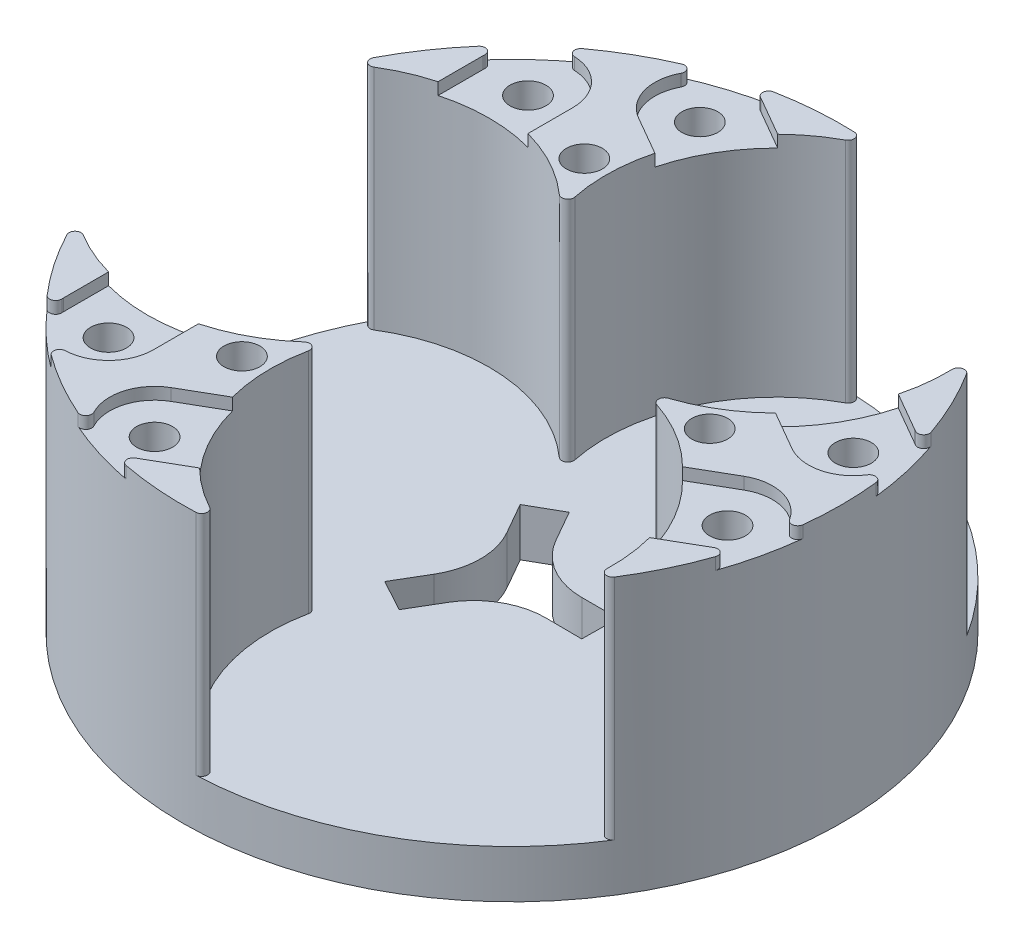
SolidWorks part; units mm, degrees
ref_plane "Front Plane" through (0, 0, 0) normal (0, 0, 1) x (1, 0, 0)
ref_plane "Top Plane" through (0, 0, 0) normal (0, 1, 0) x (1, 0, 0)
ref_plane "Right Plane" through (0, 0, 0) normal (1, 0, 0) x (0, 0, -1)
sketch "Sketch1" plane through (0, 0, 0) normal (0, 1, 0) x (1, 0, 0)
  line L0 (-16.1658, 17.5) -> (-16.1658, -17.5) construction
  line L1 (-3.4432, 3.0103) -> (-4.9292, 5.6165)
  line L2 (-4.9292, 5.6165) -> (-2.3231, 7.1024)
  line L3 (-2.3231, 7.1024) -> (-0.8371, 4.4963)
  line L4 (4.376, 1.4683) -> (7.376, 1.4687)
  line L5 (7.376, 1.4687) -> (7.3529, -1.5312)
  line L6 (7.3529, -1.5312) -> (4.353, -1.5081)
  line L7 (-0.8599, -4.4576) -> (-2.3851, -7.041)
  line L8 (-2.3851, -7.041) -> (-5.0138, -5.5954)
  line L9 (-5.0138, -5.5954) -> (-3.4887, -3.012)
  line L10 (4.3751, 7.4683) -> (0, 0) construction
  line L11 (0, 0) -> (-8.6554, 0.0384) construction
  line L12 (0, 0) -> (4.3068, -7.5079) construction
  circle A0 centre (0, 0) radius 27.5
  circle A1 centre (-16.1658, 17.5) radius 1.5
  circle A2 centre (-16.1658, -17.5) radius 1.5
  circle A3 centre (23.2383, 5.25) radius 1.5
  circle A4 centre (-7.0725, 22.75) radius 1.5
  circle A5 centre (-7.0725, -22.75) radius 1.5
  circle A6 centre (23.2383, -5.25) radius 1.5
  arc A16 (-3.4887, -3.012) -> (-3.4432, 3.0103) centre (-8.6554, 0.0384) ccw
  arc A17 (-0.8371, 4.4963) -> (4.376, 1.4683) centre (4.3751, 7.4683) ccw
  arc A18 (4.353, -1.5081) -> (-0.8599, -4.4576) centre (4.3068, -7.5079) ccw
  circle A19 centre (16.5, 0) radius 1.5
  circle A20 centre (-8.25, -14.2894) radius 1.5
  circle A21 centre (-8.25, 14.2894) radius 1.5
  point P19 (0, 0)
  dimension "D1" = 55
  dimension "D3" = 3
  dimension "D7" = 6
  dimension "D2" = 35
  dimension "D5" = 3
  dimension "D6" = 3
  dimension "D4" = 3
extrude "Boss-Extrude1" add sketch "Sketch1" along normal blind 4
sketch "Sketch2" plane through (0, 4, 0) normal (0, 1, 0) x (1, 0, 0)
  line L0 (-2.2, 0) -> (2.2, 0) construction
  arc A9 (12.569, 0.4746) -> (22.3271, 14.4056) centre (8.0829, 14) ccw
  arc A11 (23.2496, 14.6869) -> (23.2496, -14.6869) centre (0, 0) cw
  arc A22 (22.3271, 14.4056) -> (23.2496, 14.6869) centre (22.8269, 14.4198) cw
  circle A24 centre (23.2383, 5.25) radius 1.5
  circle A25 centre (23.2383, -5.25) radius 1.5
  circle A26 centre (23.2383, 5.25) radius 1.5 construction
  circle A27 centre (-7.0725, -22.75) radius 1.5
  circle A28 centre (-16.1658, -17.5) radius 1.5
  circle A29 centre (-16.1658, 17.5) radius 1.5
  circle A30 centre (-7.0725, 22.75) radius 1.5
  circle A31 centre (16.5, 0) radius 1.5
  circle A32 centre (-8.25, -14.2894) radius 1.5
  circle A33 centre (-8.25, 14.2894) radius 1.5
  arc A35 (12.569, -0.4746) -> (12.569, 0.4746) centre (12.7264, 0) cw
  arc A41 (22.3271, -14.4056) -> (23.2496, -14.6869) centre (22.8269, -14.4198) ccw
  arc A42 (12.569, -0.4746) -> (22.3271, -14.4056) centre (8.0829, -14) cw
  circle A43 centre (0, 0) radius 27.5 construction
  arc A44 (-6.6955, -10.6478) -> (-5.8735, -11.1224) centre (-6.3632, -11.0214) cw
  arc A45 (-5.8735, -11.1224) -> (1.312, -26.5387) centre (8.0829, -14) ccw
  arc A46 (1.312, -26.5387) -> (1.0944, -27.4782) centre (1.0745, -26.9786) cw
  arc A47 (1.0944, -27.4782) -> (-24.344, -12.7914) centre (0, 0) cw
  arc A48 (-23.6392, -12.1331) -> (-24.344, -12.7914) centre (-23.9014, -12.5588) ccw
  arc A49 (-6.6955, -10.6478) -> (-23.6392, -12.1331) centre (-16.1658, 0) cw
  arc A50 (-5.8735, 11.1224) -> (-6.6955, 10.6478) centre (-6.3632, 11.0214) cw
  arc A51 (-6.6955, 10.6478) -> (-23.6392, 12.1331) centre (-16.1658, 0) ccw
  arc A52 (-23.6392, 12.1331) -> (-24.344, 12.7914) centre (-23.9014, 12.5588) cw
  arc A53 (-24.344, 12.7914) -> (1.0944, 27.4782) centre (0, 0) cw
  arc A54 (1.312, 26.5387) -> (1.0944, 27.4782) centre (1.0745, 26.9786) ccw
  arc A55 (-5.8735, 11.1224) -> (1.312, 26.5387) centre (8.0829, 14) cw
  point P14 (-23.6392, 12.1331)
  point P45 (0, 0)
  point P47 (0, 0)
  dimension "D1" = 0.5
  dimension "D2" = 14.25
  dimension "D4" = 3
  dimension "D3" = 3
extrude "Boss-Extrude2" add sketch "Sketch2" along normal blind 19
sketch "Sketch3" plane through (0, 23, 0) normal (0, 1, 0) x (1, 0, 0)
  line L0 (-12.65, 0) -> (12.65, 0) construction
  line L1 (21.3633, -2.0024) -> (18.1138, -3.8785)
  line L2 (25.1133, -8.4976) -> (21.8638, -10.3737)
  line L3 (25.1133, 8.4976) -> (21.8638, 10.3737)
  line L4 (21.3633, 2.0024) -> (18.1138, 3.8785)
  line L5 (21.8638, -10.3737) -> (18.1138, -3.8785)
  line L6 (18.1138, 3.8785) -> (21.8638, 10.3737)
  line L7 (-19.9158, -13.7477) -> (-12.4158, -13.7477)
  line L8 (-12.4158, -17.5) -> (-12.4158, -13.7477)
  line L9 (-19.9158, -17.5) -> (-19.9158, -13.7477)
  line L10 (-5.698, -17.6263) -> (-1.948, -24.1215)
  line L11 (-5.1975, -25.9976) -> (-1.948, -24.1215)
  line L12 (-8.9475, -19.5024) -> (-5.698, -17.6263)
  line L13 (-1.948, 24.1215) -> (-5.698, 17.6263)
  line L14 (-8.9475, 19.5024) -> (-5.698, 17.6263)
  line L15 (-5.1975, 25.9976) -> (-1.948, 24.1215)
  line L16 (-12.4158, 13.7477) -> (-19.9158, 13.7477)
  line L17 (-19.9158, 17.5) -> (-19.9158, 13.7477)
  line L18 (-12.4158, 17.5) -> (-12.4158, 13.7477)
  arc A0 (21.3633, 2.0024) -> (25.1133, 8.4976) centre (23.2383, 5.25) ccw
  arc A1 (-12.4158, -17.5) -> (-19.9158, -17.5) centre (-16.1658, -17.5) cw
  arc A2 (21.3633, -2.0024) -> (25.1133, -8.4976) centre (23.2383, -5.25) cw
  arc A4 (-8.9475, -19.5024) -> (-5.1975, -25.9976) centre (-7.0725, -22.75) ccw
  arc A5 (-8.9475, 19.5024) -> (-5.1975, 25.9976) centre (-7.0725, 22.75) cw
  arc A6 (-12.4158, 17.5) -> (-19.9158, 17.5) centre (-16.1658, 17.5) ccw
  circle A7 centre (23.2383, 5.25) radius 1.5 construction
  arc A8 (22.3271, -14.4056) -> (12.569, -0.4746) centre (8.0829, -14) ccw construction
  arc A9 (22.3271, -14.4056) -> (12.569, -0.4746) centre (8.0829, -14) ccw construction
  point P1 (23.2383, 4.5716)
  point P2 (18.1212, -3.8859)
  point P9 (21.8591, -10.3559)
  point P39 (0, 0)
  point P40 (0, 0)
  point P45 (0, 0)
  dimension "D1" = 7.5
  dimension "D2" = 3
extrude "Cut-Extrude1" cut sketch "Sketch3" against normal blind 1
sketch "Sketch5" plane through (0, 0, 0) normal (0, -1, 0) x (1, 0, 0)
  circle A0 centre (-7.0725, 22.75) radius 2.5
  circle A1 centre (-16.1658, 17.5) radius 2.5
  circle A2 centre (23.2383, 5.25) radius 2.5
  circle A3 centre (23.2383, -5.25) radius 2.5
  circle A4 centre (-7.0725, -22.75) radius 2.5
  circle A5 centre (-16.1658, -17.5) radius 2.5
  circle A6 centre (16.5, 0) radius 2.5
  circle A7 centre (-8.25, -14.2894) radius 2.5
  circle A8 centre (-8.25, 14.2894) radius 2.5
  dimension "D1" = 5
extrude "Cut-Extrude2" cut sketch "Sketch5" against normal blind 3
fillet "Fillet1" radius 0.5 12 edges at (26.9882, 22.5, 5.2807) (26.6372, 22.5, 6.8343) (26.6372, 22.5, -6.8343) (26.9882, 22.5, -5.2807) (-19.2373, 22.5, -19.6513) (-18.0673, 22.5, -20.7321) (-7.3999, 22.5, -26.4857) (-8.9209, 22.5, -26.0128) (-18.0673, 22.5, 20.7321) (-19.2373, 22.5, 19.6513) (-7.3999, 22.5, 26.4857) (-8.9209, 22.5, 26.0128)
